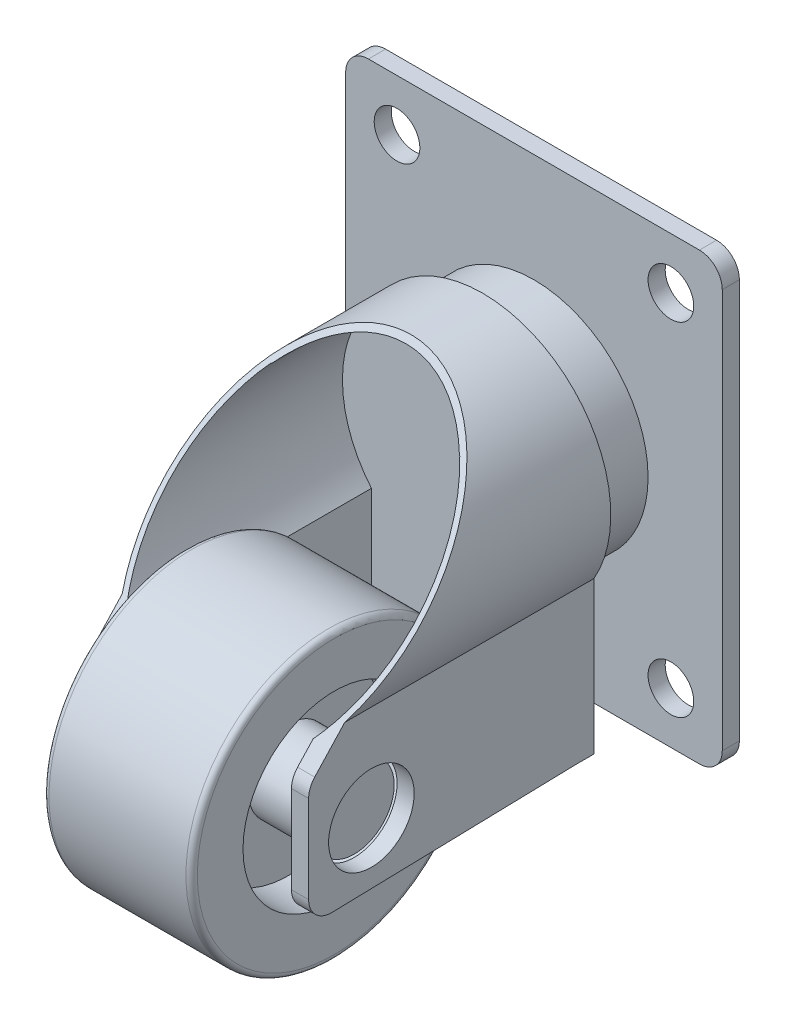
SolidWorks part; units mm, degrees
ref_plane "前视基准面" through (0, 0, 0) normal (0, 0, 1) x (1, 0, 0)
ref_plane "上视基准面" through (0, 0, 0) normal (0, 1, 0) x (1, 0, 0)
ref_plane "右视基准面" through (0, 0, 0) normal (1, 0, 0) x (0, 0, -1)
sketch "草图1" plane through (0, 0, 0) normal (0, 0, 1) x (1, 0, 0)
  line L0 (-23.7657, 25.5723) -> (-11.7657, 25.5723)
  line L1 (-11.2657, 25.0723) -> (-11.2657, 21.0723)
  line L2 (-11.2657, 21.0723) -> (-15.2657, 21.0723)
  line L3 (-15.2657, 21.0723) -> (-15.2657, 16.5723)
  line L4 (-15.2657, 16.5723) -> (-9.5157, 16.5723)
  line L8 (-26.0157, 16.5723) -> (-20.2657, 16.5723)
  line L9 (-20.2657, 16.5723) -> (-20.2657, 21.0723)
  line L10 (-20.2657, 21.0723) -> (-24.2657, 21.0723)
  line L11 (-24.2657, 21.0723) -> (-24.2657, 25.0723)
  line L12 (-9.5157, 16.5723) -> (-9.5157, 13.0723)
  line L13 (-9.5157, 13.0723) -> (-26.0157, 13.0723)
  line L14 (-26.0157, 13.0723) -> (-26.0157, 16.5723)
  line L15 (-17.7657, 13.0723) -> (-17.7657, 25.5723) construction
  arc A0 (-23.7657, 25.5723) -> (-24.2657, 25.0723) centre (-23.7657, 25.0723) ccw
  arc A1 (-11.7657, 25.5723) -> (-11.2657, 25.0723) centre (-11.7657, 25.0723) cw
  dimension "D1" = 0.5
  dimension "D2" = 0.5
revolve "旋转2" add sketch "草图1" angle 360 about L13
sketch "草图5" plane through (-9.5157, 0, 0) normal (1, 0, 0) x (0, 0, -1)
  line L1 (10.0197, 34.8049) -> (18.0053, 34.8049)
  line L4 (-5.5, 9.6236) -> (-5.5, 17.2959)
  line L5 (-4.966, 18.6564) -> (10.0197, 34.8049)
  line L9 (-3.4493, 7.6243) -> (18.0053, 8.1687)
  line L10 (18.0053, 8.1687) -> (18.0053, 34.8049)
  arc A0 (-4.966, 18.6564) -> (-5.5, 17.2959) centre (-3.5, 17.2959) ccw
  arc A1 (-3.4493, 7.6243) -> (-5.5, 9.6236) centre (-3.5, 9.6236) cw
  circle A2 centre (0, 13.0723) radius 3.75
  dimension "D1" = 2
extrude "凸台-拉伸2" add sketch "草图5" along normal blind 1.5
ref_plane "基准面1" through (-17.7657, 0, 0) normal (-1, 0, 0) x (0, 0, 1)
mirror "镜向24" about plane through (-17.7657, 0, 0) normal (-1, 0, 0) of bodies 109
sketch "草图11" plane through (0, 0, -18.0053) normal (0, 0, -1) x (-1, 0, 0)
  line L1 (8.0157, 8.1687) -> (8.0157, 34.8049) construction
  line L2 (27.5157, 8.1687) -> (27.5157, 34.8049) construction
  line L3 (8.0157, 21.4868) -> (9.0763, 20.7156)
  line L4 (27.5157, 21.4868) -> (26.455, 20.7156)
  arc A1 (8.0157, 21.4868) -> (27.5157, 21.4868) centre (17.7657, 27.0416) cw
  arc A2 (9.0763, 20.7156) -> (26.455, 20.7156) centre (17.7657, 27.0416) cw
extrude "凸台-拉伸5" add sketch "草图11" against normal blind 21.5
ref_plane "基准面2" through (0, 11.1085, 11.9704) normal (0, 0.6802, 0.733) x (1, 0, 0)
ref_plane "基准面3" through (-26.0157, 0, 0) normal (1, 0, 0) x (0, 0, -1)
sketch "草图20" plane through (-26.0157, 0, 0) normal (1, 0, 0) x (0, 0, -1)
  line L0 (-4.683, 20.4237) -> (-4.683, 39.0905)
  line L1 (-4.683, 39.0905) -> (13.9968, 39.0905)
  line L2 (0.6879, 24.749) -> (-24.6288, -2.532) construction
  line L3 (13.9968, 39.0905) -> (-4.683, 18.9613)
  line L4 (-4.683, 18.9613) -> (-4.683, 20.4237)
extrude "切除-拉伸1" cut sketch "草图20" against normal blind 4.5 and the other way blind 1.6
ref_plane "基准面4" through (-9.5157, 0, 0) normal (-1, 0, 0) x (0, 0, 1)
sketch "草图21" plane through (-9.5157, 0, 0) normal (-1, 0, 0) x (0, 0, 1)
  line L0 (4.5778, 22.482) -> (4.5778, 40.5385)
  line L1 (4.5778, 40.5385) -> (-15.3405, 40.5385)
  line L2 (24.6288, -2.532) -> (-0.6879, 24.749) construction
  line L3 (-15.3405, 40.5385) -> (4.5778, 19.0747)
  line L4 (4.5778, 19.0747) -> (4.5778, 22.482)
extrude "切除-拉伸2" cut sketch "草图21" against normal blind 7.5 and the other way blind 1.6
sketch "草图22" plane through (0, 11.1085, 11.9704) normal (0, 0.6802, 0.733) x (1, 0, 0)
  line L0 (-30.489, 39.9124) -> (-3.6719, 39.9124)
  line L1 (-3.6719, 39.9124) -> (-3.6719, 23.4148)
  line L2 (-3.6719, 23.4148) -> (-30.489, 23.4148)
  line L3 (-30.489, 23.4148) -> (-30.489, 39.9124)
extrude "切除-拉伸3" cut sketch "草图22" along normal blind 19.5
sketch "草图23" plane through (0, 0, -18.0053) normal (0, 0, -1) x (-1, 0, 0)
  line L0 (10.094, 34.5933) -> (9.969, 19.6191)
  line L1 (26.0157, 12.9279) -> (26.0157, -12.9279) construction
  line L2 (26.0023, 20.0692) -> (26.0157, 33.9982)
  arc A1 (9.969, 19.6191) -> (10.094, 34.5933) centre (17.7657, 27.0416) cw
  arc A2 (26.0157, 33.9982) -> (26.0023, 20.0692) centre (17.7657, 27.0416) cw
extrude "切除-拉伸4" cut sketch "草图23" against normal blind 27.5
sketch "草图25" plane through (0, 0, -18.0053) normal (0, 0, -1) x (-1, 0, 0)
  line L0 (6.0048, 32.4188) -> (7.656, 31.9112)
  line L1 (28.3404, 30.7957) -> (29.7456, 31.9112)
  arc A0 (6.0048, 32.4188) -> (29.7456, 31.9112) centre (17.7657, 27.0416) cw
  arc A1 (7.656, 31.9112) -> (28.3404, 30.7957) centre (17.7657, 27.0416) cw
  arc A2 (8.0157, 32.5964) -> (8.0157, 21.4868) centre (17.7657, 27.0416) ccw construction
extrude "切除-拉伸5" cut sketch "草图25" against normal blind 15.5
sketch "草图29" plane through (0, 0, -18.0053) normal (0, 0, -1) x (-1, 0, 0)
  line L0 (27.5157, 8.1687) -> (27.5157, 21.4868) construction
  line L1 (27.5157, 21.4868) -> (27.5157, 8.1687)
  line L2 (27.5157, 8.1687) -> (8.0157, 8.1687)
  line L3 (8.0157, 8.1687) -> (8.0157, 21.4868)
  arc A0 (8.0157, 21.4868) -> (27.5157, 21.4868) centre (17.7657, 27.0416) cw
extrude "凸台-拉伸6" add sketch "草图29" along normal blind 1.5
sketch "草图30" plane through (0, 0, -19.5053) normal (0, 0, -1) x (-1, 0, 0)
  circle A0 centre (17.7657, 27.0416) radius 10
extrude "凸台-拉伸7" add sketch "草图30" along normal blind 4.49
sketch "草图31" plane through (0, 0, -23.9953) normal (0, 0, -1) x (-1, 0, 0)
  line L0 (29.7657, 12.0416) -> (29.7657, 7.5416) construction
  line L1 (32.2657, 7.5416) -> (3.2657, 7.5416)
  line L2 (34.2657, 9.5416) -> (34.2657, 44.5416)
  line L3 (32.2657, 46.5416) -> (3.2657, 46.5416)
  line L4 (1.2657, 9.5416) -> (1.2657, 44.5416)
  line L5 (34.2657, 7.5416) -> (1.2657, 46.5416) construction
  line L6 (34.2657, 46.5416) -> (1.2657, 7.5416) construction
  line L7 (34.2657, 12.0416) -> (29.7657, 12.0416) construction
  line L8 (1.2657, 12.0416) -> (5.7657, 12.0416) construction
  line L9 (5.7657, 12.0416) -> (5.7657, 7.5416) construction
  line L10 (29.7657, 46.5416) -> (29.7657, 42.0416) construction
  line L11 (29.7657, 42.0416) -> (34.2657, 42.0416) construction
  circle A0 centre (29.7657, 12.0416) radius 2
  circle A1 centre (5.7657, 12.0416) radius 2
  circle A2 centre (29.7657, 42.0416) radius 2
  circle A3 centre (5.7657, 42.0416) radius 2
  arc A4 (1.2657, 44.5416) -> (3.2657, 46.5416) centre (3.2657, 44.5416) cw
  arc A5 (1.2657, 9.5416) -> (3.2657, 7.5416) centre (3.2657, 9.5416) ccw
  arc A6 (32.2657, 7.5416) -> (34.2657, 9.5416) centre (32.2657, 9.5416) ccw
  arc A7 (32.2657, 46.5416) -> (34.2657, 44.5416) centre (32.2657, 44.5416) cw
  point P0 (17.7657, 27.0416)
  dimension "D5" = 2
  dimension "D1" = 39
  dimension "D2" = 33
  dimension "D3" = 4.5
  dimension "D4" = 4.5
extrude "凸台-拉伸8" add sketch "草图31" along normal blind 1.5
ref_plane "基准面5" through (0, 0, 12.5) normal (0, 0, 1) x (1, 0, 0)
